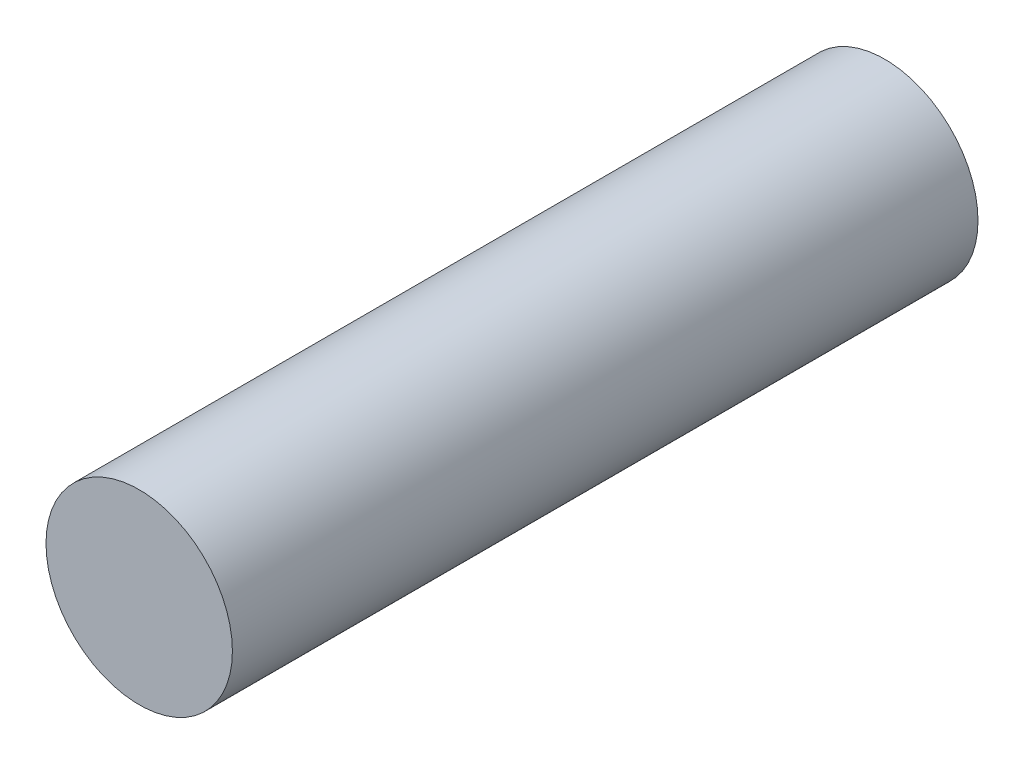
SolidWorks part; units mm, degrees
ref_plane "Face" through (0, 0, 0) normal (0, 0, 1) x (1, 0, 0)
ref_plane "Dessus" through (0, 0, 0) normal (0, 1, 0) x (1, 0, 0)
ref_plane "Droite" through (0, 0, 0) normal (1, 0, 0) x (0, 0, -1)
sketch "Esquisse1" plane through (0, 0, 0) normal (0, 0, 1) x (1, 0, 0)
  circle A0 centre (0, 0) radius 5
  dimension "D1" = 10
extrude "Extrusion1" add sketch "Esquisse1" along normal blind 40
